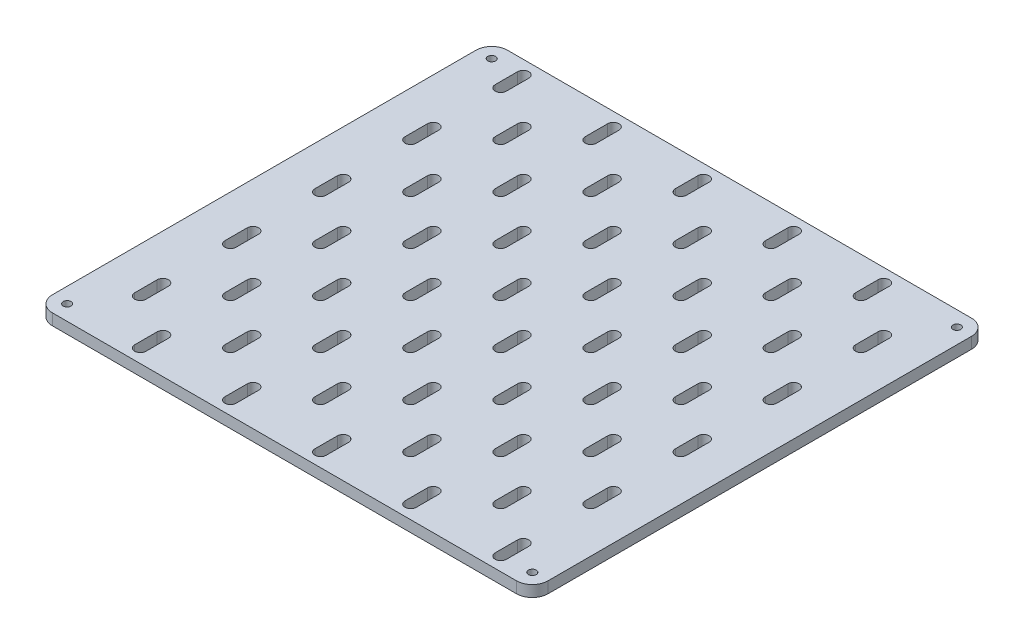
SolidWorks part; units mm, degrees
ref_plane "Front Plane" through (0, 0, 0) normal (0, 0, 1) x (1, 0, 0)
ref_plane "Top Plane" through (0, 0, 0) normal (0, 1, 0) x (1, 0, 0)
ref_plane "Right Plane" through (0, 0, 0) normal (1, 0, 0) x (0, 0, -1)
sketch "Sketch1" plane through (0, 0, 0) normal (0, 1, 0) x (1, 0, 0)
  line L0 (215, 7) -> (215, 195) construction
  line L1 (7, 0) -> (213, 0)
  line L2 (0, 7) -> (0, 195)
  line L3 (7, 202) -> (213, 202)
  line L4 (220, 7) -> (220, 195)
  line L5 (7, 5) -> (213, 5) construction
  line L6 (7, 197) -> (213, 197) construction
  line L7 (5, 7) -> (5, 195) construction
  line L8 (110, 198.5) -> (110, 3.5) construction
  line L9 (5, 101) -> (215, 101) construction
  line L10 (7, 198.5) -> (213, 198.5) construction
  line L11 (7, 3.5) -> (213, 3.5) construction
  line L12 (17.5, 3.5) -> (17.5, 198.5) construction
  line L13 (202.5, 3.5) -> (202.5, 198.5) construction
  line L14 (5, 178.5) -> (215, 178.5) construction
  line L15 (7, 202) -> (213, 202)
  line L16 (5, 23.5) -> (215, 23.5) construction
  line L17 (37.5, 3.5) -> (37.5, 198.5) construction
  line L18 (37.5, 7) -> (37.5, 195) construction
  line L19 (17.5, 7) -> (17.5, 195) construction
  line L20 (7, 23.5) -> (213, 23.5) construction
  line L21 (202.5, 7) -> (202.5, 195) construction
  line L22 (7, 178.5) -> (213, 178.5) construction
  line L23 (20, 186) -> (20, 196) construction
  line L24 (17.5, 186) -> (17.5, 196)
  line L25 (22.5, 186) -> (22.5, 196)
  line L26 (62.5, 186) -> (62.5, 196)
  line L27 (57.5, 186) -> (57.5, 196)
  line L28 (60, 186) -> (60, 196) construction
  line L29 (102.5, 186) -> (102.5, 196)
  line L30 (97.5, 186) -> (97.5, 196)
  line L31 (100, 186) -> (100, 196) construction
  line L32 (142.5, 186) -> (142.5, 196)
  line L33 (137.5, 186) -> (137.5, 196)
  line L34 (140, 186) -> (140, 196) construction
  line L35 (182.5, 186) -> (182.5, 196)
  line L36 (177.5, 186) -> (177.5, 196)
  line L37 (180, 186) -> (180, 196) construction
  line L38 (40, 176) -> (40, 166) construction
  line L39 (42.5, 176) -> (42.5, 166)
  line L40 (37.5, 176) -> (37.5, 166)
  line L41 (80, 176) -> (80, 166) construction
  line L42 (82.5, 176) -> (82.5, 166)
  line L43 (77.5, 176) -> (77.5, 166)
  line L44 (120, 176) -> (120, 166) construction
  line L45 (122.5, 176) -> (122.5, 166)
  line L46 (117.5, 176) -> (117.5, 166)
  line L47 (160, 176) -> (160, 166) construction
  line L48 (162.5, 176) -> (162.5, 166)
  line L49 (157.5, 176) -> (157.5, 166)
  line L50 (200, 176) -> (200, 166) construction
  line L51 (202.5, 176) -> (202.5, 166)
  line L52 (197.5, 176) -> (197.5, 166)
  line L53 (57.5, 146) -> (57.5, 156)
  line L54 (62.5, 146) -> (62.5, 156)
  line L55 (20, 146) -> (20, 156) construction
  line L56 (17.5, 146) -> (17.5, 156)
  line L57 (22.5, 146) -> (22.5, 156)
  line L58 (60, 146) -> (60, 156) construction
  line L59 (100, 146) -> (100, 156) construction
  line L60 (97.5, 146) -> (97.5, 156)
  line L61 (102.5, 146) -> (102.5, 156)
  line L62 (140, 146) -> (140, 156) construction
  line L63 (137.5, 146) -> (137.5, 156)
  line L64 (142.5, 146) -> (142.5, 156)
  line L65 (180, 146) -> (180, 156) construction
  line L66 (177.5, 146) -> (177.5, 156)
  line L67 (182.5, 146) -> (182.5, 156)
  line L68 (57.5, 106) -> (57.5, 116)
  line L69 (62.5, 106) -> (62.5, 116)
  line L70 (20, 106) -> (20, 116) construction
  line L71 (17.5, 106) -> (17.5, 116)
  line L72 (22.5, 106) -> (22.5, 116)
  line L73 (60, 106) -> (60, 116) construction
  line L74 (100, 106) -> (100, 116) construction
  line L75 (97.5, 106) -> (97.5, 116)
  line L76 (102.5, 106) -> (102.5, 116)
  line L77 (140, 106) -> (140, 116) construction
  line L78 (137.5, 106) -> (137.5, 116)
  line L79 (142.5, 106) -> (142.5, 116)
  line L80 (180, 106) -> (180, 116) construction
  line L81 (177.5, 106) -> (177.5, 116)
  line L82 (182.5, 106) -> (182.5, 116)
  line L83 (57.5, 66) -> (57.5, 76)
  line L84 (62.5, 66) -> (62.5, 76)
  line L85 (20, 66) -> (20, 76) construction
  line L86 (17.5, 66) -> (17.5, 76)
  line L87 (22.5, 66) -> (22.5, 76)
  line L88 (60, 66) -> (60, 76) construction
  line L89 (100, 66) -> (100, 76) construction
  line L90 (97.5, 66) -> (97.5, 76)
  line L91 (102.5, 66) -> (102.5, 76)
  line L92 (140, 66) -> (140, 76) construction
  line L93 (137.5, 66) -> (137.5, 76)
  line L94 (142.5, 66) -> (142.5, 76)
  line L95 (180, 66) -> (180, 76) construction
  line L96 (177.5, 66) -> (177.5, 76)
  line L97 (182.5, 66) -> (182.5, 76)
  line L98 (57.5, 26) -> (57.5, 36)
  line L99 (62.5, 26) -> (62.5, 36)
  line L100 (20, 26) -> (20, 36) construction
  line L101 (17.5, 26) -> (17.5, 36)
  line L102 (22.5, 26) -> (22.5, 36)
  line L103 (60, 26) -> (60, 36) construction
  line L104 (100, 26) -> (100, 36) construction
  line L105 (97.5, 26) -> (97.5, 36)
  line L106 (102.5, 26) -> (102.5, 36)
  line L107 (140, 26) -> (140, 36) construction
  line L108 (137.5, 26) -> (137.5, 36)
  line L109 (142.5, 26) -> (142.5, 36)
  line L110 (180, 26) -> (180, 36) construction
  line L111 (177.5, 26) -> (177.5, 36)
  line L112 (182.5, 26) -> (182.5, 36)
  line L113 (40, 136) -> (40, 126) construction
  line L114 (42.5, 136) -> (42.5, 126)
  line L115 (37.5, 136) -> (37.5, 126)
  line L116 (80, 136) -> (80, 126) construction
  line L117 (82.5, 136) -> (82.5, 126)
  line L118 (77.5, 136) -> (77.5, 126)
  line L119 (120, 136) -> (120, 126) construction
  line L120 (122.5, 136) -> (122.5, 126)
  line L121 (117.5, 136) -> (117.5, 126)
  line L122 (160, 136) -> (160, 126) construction
  line L123 (162.5, 136) -> (162.5, 126)
  line L124 (157.5, 136) -> (157.5, 126)
  line L125 (200, 136) -> (200, 126) construction
  line L126 (202.5, 136) -> (202.5, 126)
  line L127 (197.5, 136) -> (197.5, 126)
  line L128 (40, 96) -> (40, 86) construction
  line L129 (42.5, 96) -> (42.5, 86)
  line L130 (37.5, 96) -> (37.5, 86)
  line L131 (80, 96) -> (80, 86) construction
  line L132 (82.5, 96) -> (82.5, 86)
  line L133 (77.5, 96) -> (77.5, 86)
  line L134 (120, 96) -> (120, 86) construction
  line L135 (122.5, 96) -> (122.5, 86)
  line L136 (117.5, 96) -> (117.5, 86)
  line L137 (160, 96) -> (160, 86) construction
  line L138 (162.5, 96) -> (162.5, 86)
  line L139 (157.5, 96) -> (157.5, 86)
  line L140 (200, 96) -> (200, 86) construction
  line L141 (202.5, 96) -> (202.5, 86)
  line L142 (197.5, 96) -> (197.5, 86)
  line L143 (40, 56) -> (40, 46) construction
  line L144 (42.5, 56) -> (42.5, 46)
  line L145 (37.5, 56) -> (37.5, 46)
  line L146 (80, 56) -> (80, 46) construction
  line L147 (82.5, 56) -> (82.5, 46)
  line L148 (77.5, 56) -> (77.5, 46)
  line L149 (120, 56) -> (120, 46) construction
  line L150 (122.5, 56) -> (122.5, 46)
  line L151 (117.5, 56) -> (117.5, 46)
  line L152 (160, 56) -> (160, 46) construction
  line L153 (162.5, 56) -> (162.5, 46)
  line L154 (157.5, 56) -> (157.5, 46)
  line L155 (200, 56) -> (200, 46) construction
  line L156 (202.5, 56) -> (202.5, 46)
  line L157 (197.5, 56) -> (197.5, 46)
  line L158 (40, 16) -> (40, 6) construction
  line L159 (42.5, 16) -> (42.5, 6)
  line L160 (37.5, 16) -> (37.5, 6)
  line L161 (80, 16) -> (80, 6) construction
  line L162 (82.5, 16) -> (82.5, 6)
  line L163 (77.5, 16) -> (77.5, 6)
  line L164 (120, 16) -> (120, 6) construction
  line L165 (122.5, 16) -> (122.5, 6)
  line L166 (117.5, 16) -> (117.5, 6)
  line L167 (160, 16) -> (160, 6) construction
  line L168 (162.5, 16) -> (162.5, 6)
  line L169 (157.5, 16) -> (157.5, 6)
  line L170 (200, 16) -> (200, 6) construction
  line L171 (202.5, 16) -> (202.5, 6)
  line L172 (197.5, 16) -> (197.5, 6)
  arc A0 (7, 0) -> (0, 7) centre (7, 7) cw
  arc A1 (213, 0) -> (220, 7) centre (213, 7) ccw
  arc A2 (213, 202) -> (220, 195) centre (213, 195) cw
  arc A3 (0, 195) -> (7, 202) centre (7, 195) cw
  circle A4 centre (6.75, 195.25) radius 1.75
  circle A5 centre (213.25, 195.25) radius 1.75
  circle A6 centre (213.25, 6.75) radius 1.75
  circle A7 centre (6.75, 6.75) radius 1.75
  arc A8 (17.5, 186) -> (22.5, 186) centre (20, 186) ccw
  arc A9 (22.5, 196) -> (17.5, 196) centre (20, 196) ccw
  arc A10 (57.5, 186) -> (62.5, 186) centre (60, 186) ccw
  arc A11 (62.5, 196) -> (57.5, 196) centre (60, 196) ccw
  arc A12 (97.5, 186) -> (102.5, 186) centre (100, 186) ccw
  arc A13 (102.5, 196) -> (97.5, 196) centre (100, 196) ccw
  arc A14 (137.5, 186) -> (142.5, 186) centre (140, 186) ccw
  arc A15 (142.5, 196) -> (137.5, 196) centre (140, 196) ccw
  arc A16 (177.5, 186) -> (182.5, 186) centre (180, 186) ccw
  arc A17 (182.5, 196) -> (177.5, 196) centre (180, 196) ccw
  arc A18 (42.5, 176) -> (37.5, 176) centre (40, 176) ccw
  arc A19 (37.5, 166) -> (42.5, 166) centre (40, 166) ccw
  arc A20 (82.5, 176) -> (77.5, 176) centre (80, 176) ccw
  arc A21 (77.5, 166) -> (82.5, 166) centre (80, 166) ccw
  arc A22 (122.5, 176) -> (117.5, 176) centre (120, 176) ccw
  arc A23 (117.5, 166) -> (122.5, 166) centre (120, 166) ccw
  arc A24 (162.5, 176) -> (157.5, 176) centre (160, 176) ccw
  arc A25 (157.5, 166) -> (162.5, 166) centre (160, 166) ccw
  arc A26 (202.5, 176) -> (197.5, 176) centre (200, 176) ccw
  arc A27 (197.5, 166) -> (202.5, 166) centre (200, 166) ccw
  arc A28 (62.5, 156) -> (57.5, 156) centre (60, 156) ccw
  arc A29 (57.5, 146) -> (62.5, 146) centre (60, 146) ccw
  arc A30 (17.5, 146) -> (22.5, 146) centre (20, 146) ccw
  arc A31 (22.5, 156) -> (17.5, 156) centre (20, 156) ccw
  arc A32 (97.5, 146) -> (102.5, 146) centre (100, 146) ccw
  arc A33 (102.5, 156) -> (97.5, 156) centre (100, 156) ccw
  arc A34 (137.5, 146) -> (142.5, 146) centre (140, 146) ccw
  arc A35 (142.5, 156) -> (137.5, 156) centre (140, 156) ccw
  arc A36 (177.5, 146) -> (182.5, 146) centre (180, 146) ccw
  arc A37 (182.5, 156) -> (177.5, 156) centre (180, 156) ccw
  arc A38 (62.5, 116) -> (57.5, 116) centre (60, 116) ccw
  arc A39 (57.5, 106) -> (62.5, 106) centre (60, 106) ccw
  arc A40 (17.5, 106) -> (22.5, 106) centre (20, 106) ccw
  arc A41 (22.5, 116) -> (17.5, 116) centre (20, 116) ccw
  arc A42 (97.5, 106) -> (102.5, 106) centre (100, 106) ccw
  arc A43 (102.5, 116) -> (97.5, 116) centre (100, 116) ccw
  arc A44 (137.5, 106) -> (142.5, 106) centre (140, 106) ccw
  arc A45 (142.5, 116) -> (137.5, 116) centre (140, 116) ccw
  arc A46 (177.5, 106) -> (182.5, 106) centre (180, 106) ccw
  arc A47 (182.5, 116) -> (177.5, 116) centre (180, 116) ccw
  arc A48 (62.5, 76) -> (57.5, 76) centre (60, 76) ccw
  arc A49 (57.5, 66) -> (62.5, 66) centre (60, 66) ccw
  arc A50 (17.5, 66) -> (22.5, 66) centre (20, 66) ccw
  arc A51 (22.5, 76) -> (17.5, 76) centre (20, 76) ccw
  arc A52 (97.5, 66) -> (102.5, 66) centre (100, 66) ccw
  arc A53 (102.5, 76) -> (97.5, 76) centre (100, 76) ccw
  arc A54 (137.5, 66) -> (142.5, 66) centre (140, 66) ccw
  arc A55 (142.5, 76) -> (137.5, 76) centre (140, 76) ccw
  arc A56 (177.5, 66) -> (182.5, 66) centre (180, 66) ccw
  arc A57 (182.5, 76) -> (177.5, 76) centre (180, 76) ccw
  arc A58 (62.5, 36) -> (57.5, 36) centre (60, 36) ccw
  arc A59 (57.5, 26) -> (62.5, 26) centre (60, 26) ccw
  arc A60 (17.5, 26) -> (22.5, 26) centre (20, 26) ccw
  arc A61 (22.5, 36) -> (17.5, 36) centre (20, 36) ccw
  arc A62 (97.5, 26) -> (102.5, 26) centre (100, 26) ccw
  arc A63 (102.5, 36) -> (97.5, 36) centre (100, 36) ccw
  arc A64 (137.5, 26) -> (142.5, 26) centre (140, 26) ccw
  arc A65 (142.5, 36) -> (137.5, 36) centre (140, 36) ccw
  arc A66 (177.5, 26) -> (182.5, 26) centre (180, 26) ccw
  arc A67 (182.5, 36) -> (177.5, 36) centre (180, 36) ccw
  arc A68 (42.5, 136) -> (37.5, 136) centre (40, 136) ccw
  arc A69 (37.5, 126) -> (42.5, 126) centre (40, 126) ccw
  arc A70 (82.5, 136) -> (77.5, 136) centre (80, 136) ccw
  arc A71 (77.5, 126) -> (82.5, 126) centre (80, 126) ccw
  arc A72 (122.5, 136) -> (117.5, 136) centre (120, 136) ccw
  arc A73 (117.5, 126) -> (122.5, 126) centre (120, 126) ccw
  arc A74 (162.5, 136) -> (157.5, 136) centre (160, 136) ccw
  arc A75 (157.5, 126) -> (162.5, 126) centre (160, 126) ccw
  arc A76 (202.5, 136) -> (197.5, 136) centre (200, 136) ccw
  arc A77 (197.5, 126) -> (202.5, 126) centre (200, 126) ccw
  arc A78 (42.5, 96) -> (37.5, 96) centre (40, 96) ccw
  arc A79 (37.5, 86) -> (42.5, 86) centre (40, 86) ccw
  arc A80 (82.5, 96) -> (77.5, 96) centre (80, 96) ccw
  arc A81 (77.5, 86) -> (82.5, 86) centre (80, 86) ccw
  arc A82 (122.5, 96) -> (117.5, 96) centre (120, 96) ccw
  arc A83 (117.5, 86) -> (122.5, 86) centre (120, 86) ccw
  arc A84 (162.5, 96) -> (157.5, 96) centre (160, 96) ccw
  arc A85 (157.5, 86) -> (162.5, 86) centre (160, 86) ccw
  arc A86 (202.5, 96) -> (197.5, 96) centre (200, 96) ccw
  arc A87 (197.5, 86) -> (202.5, 86) centre (200, 86) ccw
  arc A88 (42.5, 56) -> (37.5, 56) centre (40, 56) ccw
  arc A89 (37.5, 46) -> (42.5, 46) centre (40, 46) ccw
  arc A90 (82.5, 56) -> (77.5, 56) centre (80, 56) ccw
  arc A91 (77.5, 46) -> (82.5, 46) centre (80, 46) ccw
  arc A92 (122.5, 56) -> (117.5, 56) centre (120, 56) ccw
  arc A93 (117.5, 46) -> (122.5, 46) centre (120, 46) ccw
  arc A94 (162.5, 56) -> (157.5, 56) centre (160, 56) ccw
  arc A95 (157.5, 46) -> (162.5, 46) centre (160, 46) ccw
  arc A96 (202.5, 56) -> (197.5, 56) centre (200, 56) ccw
  arc A97 (197.5, 46) -> (202.5, 46) centre (200, 46) ccw
  arc A98 (42.5, 16) -> (37.5, 16) centre (40, 16) ccw
  arc A99 (37.5, 6) -> (42.5, 6) centre (40, 6) ccw
  arc A100 (82.5, 16) -> (77.5, 16) centre (80, 16) ccw
  arc A101 (77.5, 6) -> (82.5, 6) centre (80, 6) ccw
  arc A102 (122.5, 16) -> (117.5, 16) centre (120, 16) ccw
  arc A103 (117.5, 6) -> (122.5, 6) centre (120, 6) ccw
  arc A104 (162.5, 16) -> (157.5, 16) centre (160, 16) ccw
  arc A105 (157.5, 6) -> (162.5, 6) centre (160, 6) ccw
  arc A106 (202.5, 16) -> (197.5, 16) centre (200, 16) ccw
  arc A107 (197.5, 6) -> (202.5, 6) centre (200, 6) ccw
  point P7 (0, 0)
  point P10 (220, 0)
  point P15 (0, 202)
  point P56 (110, 202)
  point P65 (20, 191)
  point P73 (60, 191)
  point P80 (100, 191)
  point P87 (140, 191)
  point P94 (180, 191)
  point P100 (40, 171)
  point P109 (80, 171)
  point P116 (120, 171)
  point P123 (160, 171)
  point P130 (200, 171)
  point P137 (20, 151)
  point P144 (60, 151)
  point P151 (100, 151)
  point P158 (140, 151)
  point P165 (180, 151)
  point P172 (20, 111)
  point P179 (60, 111)
  point P186 (100, 111)
  point P193 (140, 111)
  point P200 (180, 111)
  point P207 (20, 71)
  point P214 (60, 71)
  point P221 (100, 71)
  point P228 (140, 71)
  point P235 (180, 71)
  point P242 (20, 31)
  point P249 (60, 31)
  point P256 (100, 31)
  point P263 (140, 31)
  point P270 (180, 31)
  point P277 (40, 131)
  point P284 (80, 131)
  point P291 (120, 131)
  point P298 (160, 131)
  point P305 (200, 131)
  point P312 (40, 91)
  point P319 (80, 91)
  point P326 (120, 91)
  point P333 (160, 91)
  point P340 (200, 91)
  point P347 (40, 51)
  point P354 (80, 51)
  point P361 (120, 51)
  point P368 (160, 51)
  point P375 (200, 51)
  point P382 (40, 11)
  point P389 (80, 11)
  point P396 (120, 11)
  point P403 (160, 11)
  point P410 (200, 11)
  dimension "D3" = 7
  dimension "D4" = 3.5
  dimension "D14" = 2.5
  dimension "D18" = 2.5
  dimension "D1" = 202
  dimension "D2" = 220
  dimension "D15" = 10
  dimension "D17" = 40
  dimension "D19" = 10
  dimension "D21" = 40
  dimension "D23" = 40
  dimension "D25" = 40
  dimension "D5" = 5
  dimension "D6" = 5
  dimension "D7" = 3.5
  dimension "D8" = 3.5
  dimension "D9" = 17.5
  dimension "D10" = 17.5
  dimension "D11" = 23.5
  dimension "D12" = 23.5
  dimension "D13" = 37.5
  dimension "D16" = 5
  dimension "D20" = 5
  dimension "D22" = 5
  dimension "D24" = 5
extrude "Boss-Extrude1" add sketch "Sketch1" along normal blind 5 contours A3 L2 A0 L1 A1 L4 A2 L3 A107 L172 A106 L171 A105 L169 A104 L168 A103 L166 A102 L165 A101 L163 A100 L162 A99 L160 A98 L159 A97 L157 A96 L156 A95 L154 A94 L153 A93 L151 A92 L150 A91 L148
hole_wizard "CSK for M3 Countersunk Flat Head Screw1" positions "3DSketch1" profile "Sketch2" countersink size "M3" standard "DIN"
sketch3d "3DSketch1"
  line L0 (6.75, 5, -6.75) -> (6.75, 0, -6.75) construction
  line L1 (213.25, 5, -6.75) -> (213.25, 0, -6.75) construction
  line L2 (6.75, 5, -195.25) -> (6.75, 0, -195.25) construction
  line L3 (213.25, 5, -195.25) -> (213.25, 0, -195.25) construction
  point P0 (6.75, 0, -6.75)
  point P4 (213.25, 0, -6.75)
  point P8 (6.75, 0, -195.25)
  point P12 (213.25, 0, -195.25)
sketch "Sketch2" plane through (6.75, 0, -6.75) normal (1, 0, 0) x (0, 0, -1)
  line L0 (0, 0) -> (0, 4.9614)
  line L1 (0, 4.9614) -> (1.6, 4)
  line L2 (1.6, 4) -> (1.6, 1.55)
  line L3 (1.6, 1.55) -> (3.15, 0)
  line L5 (3.15, 0) -> (0, 0)
  line L6 (-1.6, 1.55) -> (-3.15, 0) construction
  line L10 (0, 4.9614) -> (-1.6, 4) construction
  line L11 (0, -6.35) -> (0, 107.95) construction
  dimension "Hole Dia." = 3.2
  dimension "Hole Depth" = 4
  dimension "Near C'Sink Dia." = 6.3
  dimension "Near C'Sink Angle" = 90
  dimension "Drill Angle" = 118
